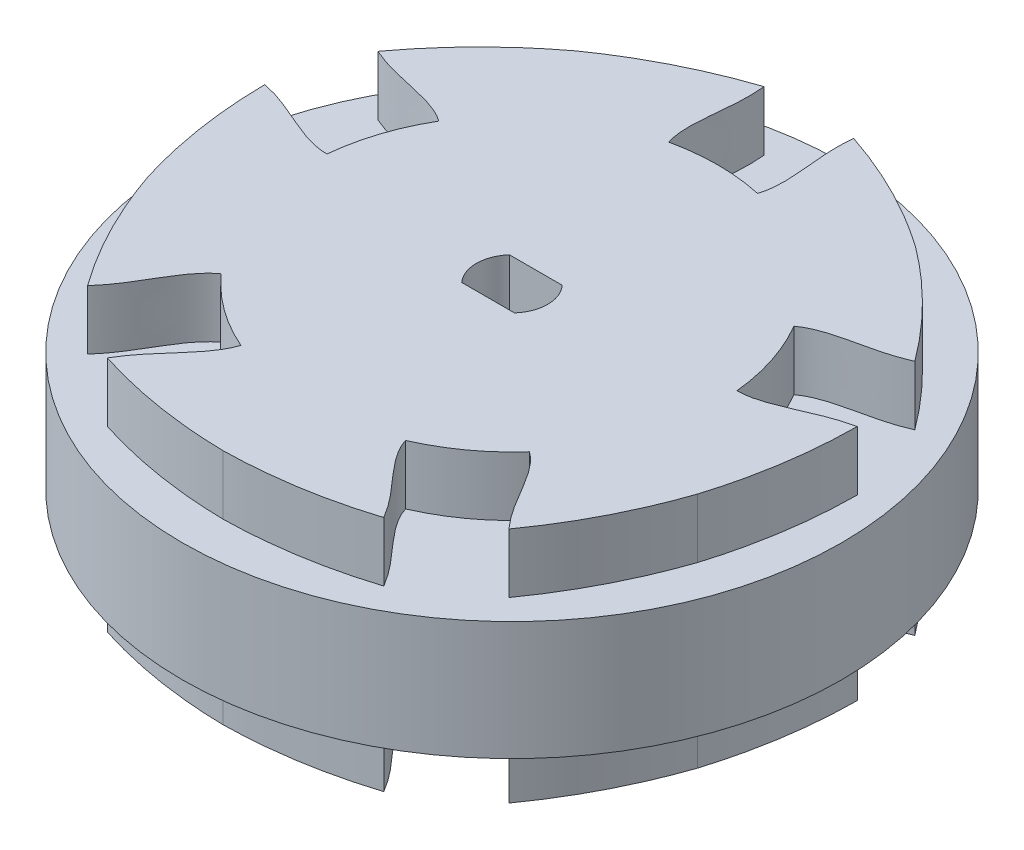
SolidWorks part; units mm, degrees
ref_plane "Front Plane" through (0, 0, 0) normal (0, 0, 1) x (1, 0, 0)
ref_plane "Top Plane" through (0, 0, 0) normal (0, 1, 0) x (1, 0, 0)
ref_plane "Right Plane" through (0, 0, 0) normal (1, 0, 0) x (0, 0, -1)
sketch "Sketch1" plane through (0, 0, 0) normal (0, 1, 0) x (1, 0, 0)
  line L0 (0, 20.9267) -> (0, -30.1304) construction
  line L1 (-41.7081, 0) -> (48.7066, 0) construction
  circle A1 centre (0, 0) radius 15.6172
  circle A2 centre (0, 0) radius 24.921
  spline S0 degree 3 poles (10.482, -20.2061) (9.1008, -17.8075) (6.885, -16.3334) (6.2419, -14.3155) knots 0.184964 0.184964 0.184964 0.184964 1 1 1 1
  spline S1 degree 3 poles (-10.482, -20.2061) (-9.1008, -17.8075) (-6.885, -16.3334) (-6.2419, -14.3155) knots 0.184964 0.184964 0.184964 0.184964 1 1 1 1
  spline S2 degree 2 poles (-10.482, -20.2061) (-5.36, -21.8269) (0, -21.9059) knots 0 0 0 1 1 1
  spline S3 degree 3 poles (-15.978, -16.213) (-14.1237, -14.1582) (-13.4064, -11.5953) (-11.686, -10.3602) knots 0.184964 0.184964 0.184964 0.184964 1 1 1 1
  spline S4 degree 3 poles (-22.4563, 3.725) (-19.7483, 3.1525) (-17.6616, 1.5007) (-15.5437, 1.5127) knots 0.184964 0.184964 0.184964 0.184964 1 1 1 1
  spline S5 degree 2 poles (-22.4563, 3.725) (-22.415, -1.6472) (-20.8337, -6.7693) knots 0 0 0 1 1 1
  spline S6 degree 2 poles (-15.978, -16.213) (-19.1023, -11.8426) (-20.8337, -6.7693) knots 0 0 0 1 1 1
  spline S7 degree 3 poles (-20.357, 10.1859) (-17.8297, 9.0573) (-15.1706, 9.1671) (-13.4643, 7.9126) knots 0.184964 0.184964 0.184964 0.184964 1 1 1 1
  spline S8 degree 3 poles (-3.3967, 22.5083) (-3.1043, 19.7559) (-4.0305, 17.2609) (-3.3646, 15.2504) knots 0.184964 0.184964 0.184964 0.184964 1 1 1 1
  spline S9 degree 2 poles (-3.3967, 22.5083) (-8.4932, 20.8089) (-12.876, 17.7222) knots 0 0 0 1 1 1
  spline S10 degree 2 poles (-20.357, 10.1859) (-17.1659, 14.5078) (-12.876, 17.7222) knots 0 0 0 1 1 1
  spline S11 degree 3 poles (3.3967, 22.5083) (3.1043, 19.7559) (4.0305, 17.2609) (3.3646, 15.2504) knots 0.184964 0.184964 0.184964 0.184964 1 1 1 1
  spline S12 degree 3 poles (20.357, 10.1859) (17.8297, 9.0573) (15.1706, 9.1671) (13.4643, 7.9126) knots 0.184964 0.184964 0.184964 0.184964 1 1 1 1
  spline S13 degree 2 poles (20.357, 10.1859) (17.1659, 14.5078) (12.876, 17.7222) knots 0 0 0 1 1 1
  spline S14 degree 2 poles (3.3967, 22.5083) (8.4932, 20.8089) (12.876, 17.7222) knots 0 0 0 1 1 1
  spline S15 degree 2 poles (10.482, -20.2061) (5.36, -21.8269) (0, -21.9059) knots 0 0 0 1 1 1
  spline S16 degree 3 poles (22.4563, 3.725) (19.7483, 3.1525) (17.6616, 1.5007) (15.5437, 1.5127) knots 0.184964 0.184964 0.184964 0.184964 1 1 1 1
  spline S17 degree 3 poles (15.978, -16.213) (14.1237, -14.1582) (13.4064, -11.5953) (11.686, -10.3602) knots 0.184964 0.184964 0.184964 0.184964 1 1 1 1
  spline S18 degree 2 poles (15.978, -16.213) (19.1023, -11.8426) (20.8337, -6.7693) knots 0 0 0 1 1 1
  spline S19 degree 2 poles (22.4563, 3.725) (22.415, -1.6472) (20.8337, -6.7693) knots 0 0 0 1 1 1
  point P46 (0, 0)
  point P56 (0, 0)
  point P57 (0, 0)
extrude "Boss-Extrude2" add sketch "Sketch1" along normal blind 18 contours S15 S0 A1 S1 S2 | A1 | S6 S3 A1 S4 S5 | S10 S7 A1 S8 S9 | S14 S11 A1 S12 S13 | S19 S16 A1 S17 S18
sketch "Sketch3" plane through (0, 18, 0) normal (0, 1, 0) x (1, 0, 0)
  circle A0 centre (0, 0) radius 25
  dimension "D1" = 50
extrude "Boss-Extrude3" add sketch "Sketch3" against normal blind 9 from offset 4.5 offset against normal yes
sketch "Sketch4" plane through (0, 18, 0) normal (0, 1, 0) x (1, 0, 0)
  line L0 (-2, 1.8138) -> (2, 1.8138)
  line L1 (-7.3468, 0) -> (6.249, 0) construction
  line L2 (-2, -1.8138) -> (2, -1.8138)
  arc A0 (-2, 1.8138) -> (-2, -1.8138) centre (0, 0) ccw
  arc A1 (2, -1.8138) -> (2, 1.8138) centre (0, 0) ccw
  dimension "D1" = 5.4
  dimension "D2" = 4
extrude "Cut-Extrude1" cut sketch "Sketch4" along a picked direction on the side against the normal up to surface (18 mm away) up to plane "Top Plane"
